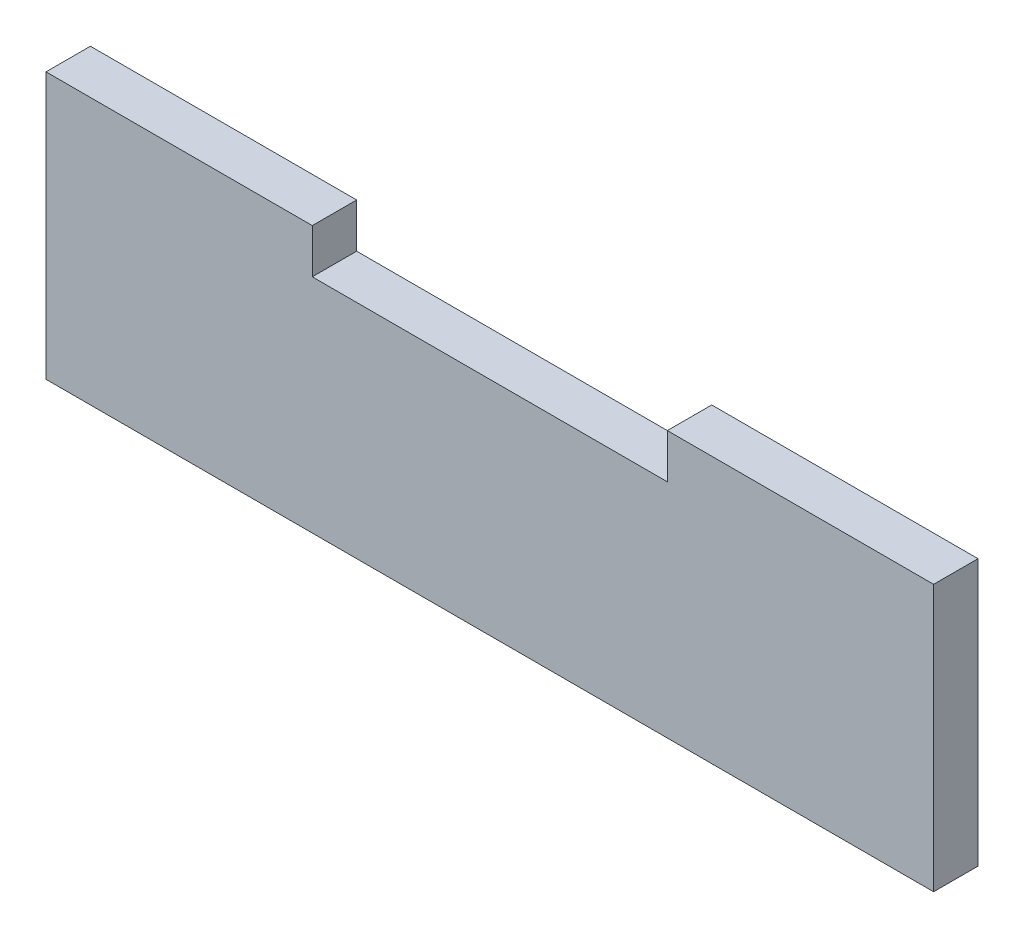
SolidWorks part; units mm, degrees
ref_plane "Front Plane" through (0, 0, 0) normal (0, 0, 1) x (1, 0, 0)
ref_plane "Top Plane" through (0, 0, 0) normal (0, 1, 0) x (1, 0, 0)
ref_plane "Right Plane" through (0, 0, 0) normal (1, 0, 0) x (0, 0, -1)
sketch "Sketch1" plane through (0, 0, 0) normal (0, 0, 1) x (1, 0, 0)
  line L0 (-50, -10.5277) -> (50, -10.5277)
  line L1 (-50, -10.5277) -> (-50, 19.4723)
  line L2 (-50, 19.4723) -> (-20, 19.4723)
  line L3 (50, -10.5277) -> (50, 19.4723)
  line L4 (-50, -10.5277) -> (50, 19.4723) construction
  line L5 (-50, 19.4723) -> (50, -10.5277) construction
  line L6 (-35, 7.7994) -> (-35, -19.4723) construction
  line L7 (-20, 19.4723) -> (-20, 14.4723)
  line L8 (-20, 14.4723) -> (20, 14.4723)
  line L9 (20, 19.4723) -> (50, 19.4723)
  line L10 (20, 14.4723) -> (20, 19.4723)
  point P0 (0, 4.4723)
  dimension "D1" = 5
extrude "Boss-Extrude1" add sketch "Sketch1" along normal blind 5
